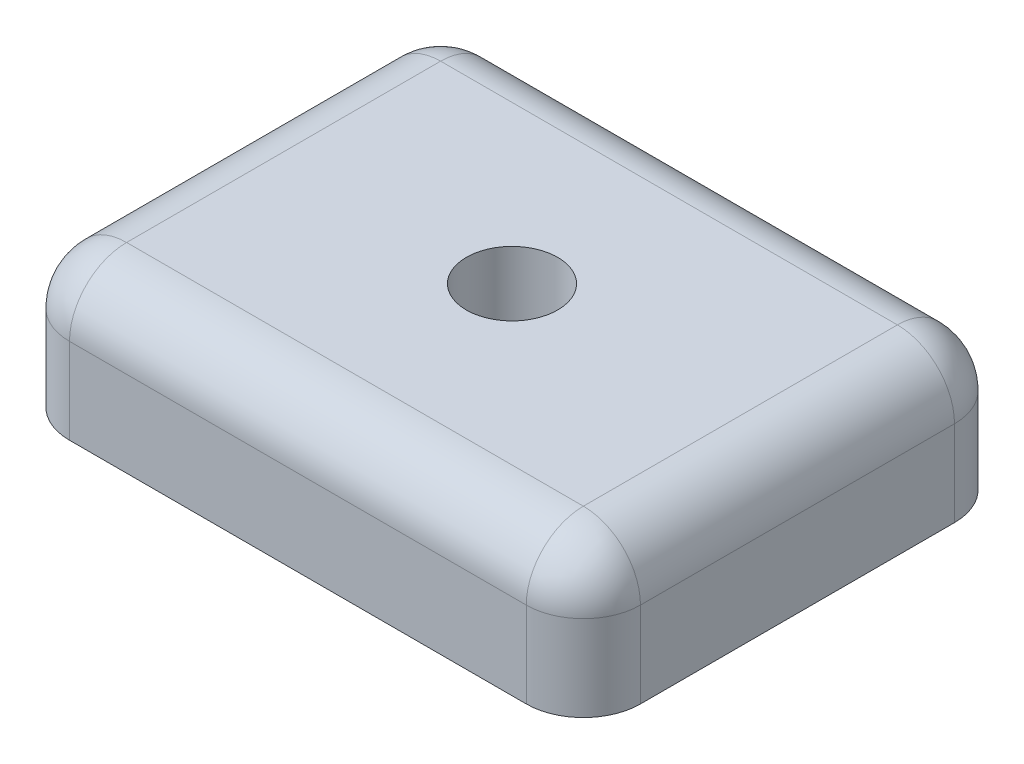
SolidWorks part; units mm, degrees
ref_plane "Front Plane" through (0, 0, 0) normal (0, 0, 1) x (1, 0, 0)
ref_plane "Top Plane" through (0, 0, 0) normal (0, 1, 0) x (1, 0, 0)
ref_plane "Right Plane" through (0, 0, 0) normal (1, 0, 0) x (0, 0, -1)
sketch "Sketch2" plane through (0, 0, 0) normal (0, 1, 0) x (1, 0, 0)
  line L0 (0, 15) -> (20, 15)
  line L1 (0, 0) -> (20, 0)
  line L2 (0, 0) -> (0, 15)
  line L4 (20, 0) -> (20, 15)
  dimension "D1" = 20
  dimension "D3" = 15
extrude "Boss-Extrude1" add sketch "Sketch2" along normal blind 5 contours L4 L0 L2 L1
sketch "Sketch3" plane through (0, 5, 0) normal (0, 1, 0) x (1, 0, 0)
  line L0 (0, 0) -> (20, 15) construction
  circle A0 centre (10, 7.5) radius 1.6
  dimension "D1" = 3.2
extrude "Cut-Extrude1" cut sketch "Sketch3" against normal through all
fillet "Fillet1" radius 2 8 edges at (0, 2.5, -15) (20, 2.5, -15) (20, 2.5, 0) (0, 2.5, 0) (10, 5, 0) (20, 5, -7.5) (10, 5, -15) (0, 5, -7.5)
